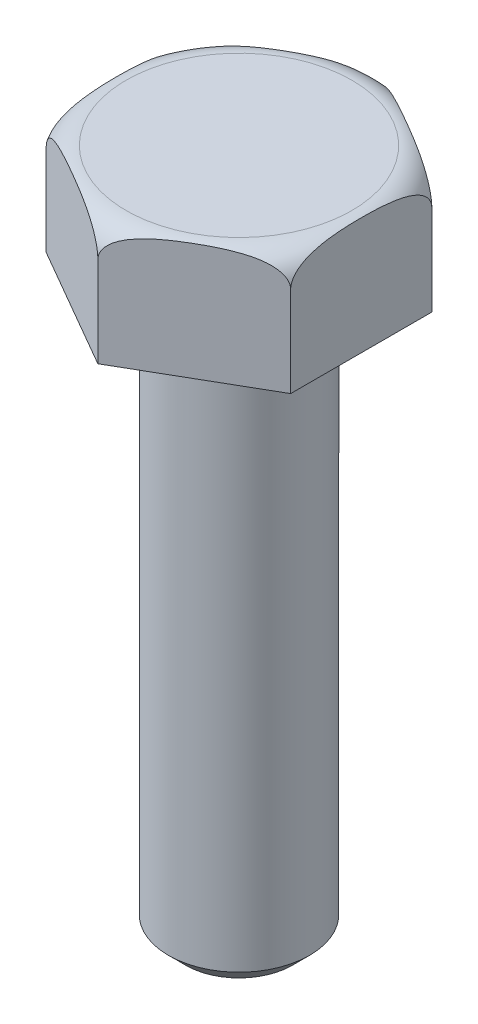
SolidWorks part; units mm, degrees
material "Chrome Stainless Steel"
ref_plane "Front" through (0, 0, 0) normal (0, 0, 1) x (1, 0, 0)
ref_plane "Top" through (0, 0, 0) normal (0, 1, 0) x (1, 0, 0)
ref_plane "Right" through (0, 0, 0) normal (1, 0, 0) x (0, 0, -1)
sketch "Sketch1" plane through (0, 0, 0) normal (0, 1, 0) x (1, 0, 0)
  line L1 (0, 6.35) -> (-5.4993, 3.175)
  line L2 (-5.4993, 3.175) -> (-5.4993, -3.175)
  line L3 (-5.4993, -3.175) -> (0, -6.35)
  line L4 (0, -6.35) -> (5.4993, -3.175)
  line L5 (5.4993, -3.175) -> (5.4993, 3.175)
  line L6 (5.4993, 3.175) -> (0, 6.35)
  circle A0 centre (0, 0) radius 6.35 construction
  dimension "D1" = 12.7
extrude "Extrude1" add sketch "Sketch1" along normal blind 5.334
sketch "Sketch3" plane through (0, 0, 0) normal (0, -1, 0) x (1, 0, 0)
  circle A0 centre (0, 0) radius 3.175
  dimension "D1" = 6.35
extrude "Extrude2" add sketch "Sketch3" along normal blind 25.4
cosmetic thread "Cosmetic Thread1" parameters "D2"=5.08
sketch "Sketch2" plane through (0, 0, 0) normal (1, 0, 0) x (0, 0, -1)
  line L0 (5.08, 5.334) -> (6.35, 5.334)
  line L1 (3.175, 5.334) -> (6.35, 5.334) construction
  line L2 (6.35, 4.064) -> (6.35, 5.334)
  line L3 (6.35, 5.334) -> (6.35, 0) construction
  arc A0 (5.08, 5.334) -> (6.35, 4.064) centre (5.08, 4.064) cw
  dimension "D1" = 1.27
revolve "Cut-Revolve1" cut sketch "Sketch2" angle 360 about axis through (0, -25.4, 0) along (0, 1, 0)
chamfer "Chamfer1" distance 0.762 angle 45 1 edges at (0, -25.4, -3.175)
